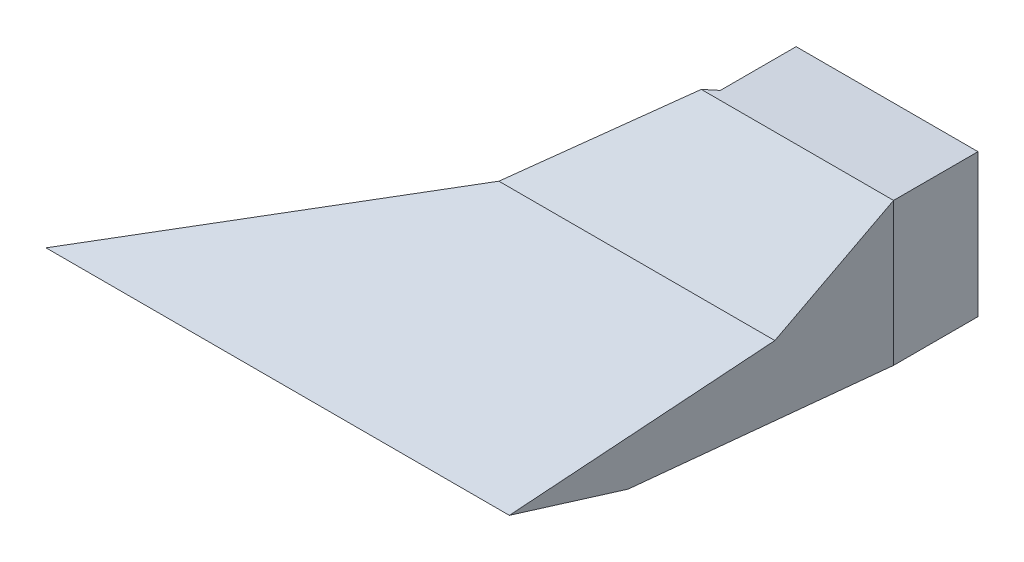
SolidWorks part; units mm, degrees
ref_plane "Front"
ref_plane "Top" through (0, 0, 0) normal (0, 1, 0) x (1, 0, 0)
ref_plane "Right" through (0, 0, 0) normal (1, 0, 0) x (0, 0, -1)
sketch "Side base sketch" plane through (0, 0, 0) normal (-1, 0, 0) x (0, 0, 1)
  line L0 (0, 13.2) -> (8.4913, 5)
  line L1 (0, 0) -> (6, -1)
  line L2 (6, -1) -> (19, -3.1667)
  line L3 (8.4913, 5) -> (19.4913, 0.803)
  line L4 (19.4913, 0.803) -> (27.4913, -2.2493)
  line L5 (27.4913, -2.2493) -> (19, -3.1667)
  line L6 (0, 13.2) -> (0, 0)
  dimension "D1" = 6
  dimension "D2" = 6
  dimension "D3" = 1
  dimension "D4" = 46
  dimension "D5" = 13
  dimension "D6" = 11
  dimension "D7" = 4
  dimension "D8" = 8
  dimension "D9" = 13.2
extrude "Side base" add sketch "Side base sketch" against normal blind 0.8
pattern_linear "Side base 2" count 2 spacing 50 along (1, 0, 0) of bodies 108
sketch "Wall base sketch" plane through (0.8, 0, 0) normal (1, 0, 0) x (0, 0, -1)
  line L0 (0, 12.0879) -> (-8.0533, 4.3109)
  line L1 (-8.0533, 4.3109) -> (-25.7424, -2.4382)
  line L3 (-19, -3.4019) -> (-19, 4.6777) construction
  line L4 (0, 13.2) -> (0, 0) construction
  line L5 (0, 0) -> (-19, -3.1667) construction
  line L8 (-8.4913, 5) -> (0, 13.2) construction
  line L9 (0, 0.811) -> (-19, -2.3556)
  line L11 (-19, -2.3556) -> (-19, -3.1667)
  line L12 (-19, -3.1667) -> (0, 0)
  line L13 (0, 0) -> (0, 0.811)
  line L14 (-25.7424, -2.4382) -> (-27.4913, -2.2493)
  line L15 (-27.4913, -2.2493) -> (-8.4913, 5)
  line L16 (-8.4913, 5) -> (0, 13.2)
  line L17 (0, 13.2) -> (0, 12.0879)
  line L18 (-19, -3.1667) -> (-27.4913, -2.2493) construction
  dimension "D1" = 0.8
  dimension "D2" = 0.8
  dimension "D3" = 0.8
extrude "Front back walls" add sketch "Wall base sketch" along normal up to next (50 mm away)
sketch "Base sketch" plane through (0, 0, 0) normal (0, 0, -1) x (-1, 0, 0)
  line L0 (-50, 12.0879) -> (-0.8, 12.0879) construction
  line L1 (0, 13.2) -> (-50.8, 13.2)
  line L2 (0, 13.2) -> (0, 0)
  line L3 (0, 0) -> (-50.8, 0)
  line L4 (-50.8, 13.2) -> (-50.8, 0)
  line L5 (-50, 0.811) -> (-34.8, 0.811)
  line L6 (-50, 0.811) -> (-50, 12.0879)
  line L7 (-50, 12.0879) -> (-34.8, 12.0879)
  line L8 (-34.8, 0.811) -> (-34.8, 12.0879)
  dimension "D1" = 15.2
extrude "Base" add sketch "Base sketch" along normal blind 0.8
sketch "Attachment base sketch" plane through (0, 0, -0.8) normal (0, 0, -1) x (-1, 0, 0)
  line L0 (-50.8, 0) -> (0, 0) construction
  line L1 (-50.8, 13.2) -> (-34, 13.2)
  line L2 (-50.8, 13.2) -> (-50.8, 0)
  line L3 (-50.8, 0) -> (-34, 0)
  line L4 (-34, 13.2) -> (-34, 0)
  line L5 (-34.8, 0.811) -> (-34.8, 12.0879) construction
  line L7 (-34.8, 12.0879) -> (-50, 12.0879)
  line L8 (-34.8, 12.0879) -> (-34.8, 0.811)
  line L9 (-34.8, 0.811) -> (-50, 0.811)
  line L10 (-50, 12.0879) -> (-50, 0.811)
  dimension "D1" = 0.8
extrude "Attachment base" add sketch "Attachment base sketch" along normal blind 7
sketch "Sketch4" plane through (0.8, 0, 0) normal (1, 0, 0) x (0, 0, -1)
  line L0 (-25.7424, -2.4382) -> (-19, -3.1667)
  line L1 (-19, -3.1667) -> (-19, -2.3556)
  line L2 (-19, -2.3556) -> (0, 0.811)
  line L3 (0, 0.811) -> (0, 12.0879)
  line L4 (-8.0533, 4.3109) -> (0, 12.0879) construction
  line L5 (0, 12.0879) -> (0, 0.811) construction
  line L6 (0, 12.0879) -> (-8.0533, 4.3109)
  line L7 (-8.0533, 4.3109) -> (-25.7424, -2.4382)
extrude "Left right wall removal" cut sketch "Sketch4" against normal through all both and the other way through all
ref_point "Cutaway left intersection point" parameters "D1"=8
ref_plane "Cutaway left plane" through (46.834, 0, 13.6287) normal (0.9602, 0, 0.2794) x (0.2794, 0, -0.9602)
sketch "Sketch6" plane through (46.834, 0, 13.6287) normal (0.9602, 0, 0.2794) x (0.2794, 0, -0.9602)
  line L1 (-14.4376, -3.1667) -> (14.1941, -3.1667)
  line L2 (-14.4376, -3.1667) -> (-14.4376, 13.2)
  line L3 (-14.4376, 13.2) -> (14.1941, 13.2)
  line L4 (14.1941, -3.1667) -> (14.1941, 13.2)
  point P4 (-14.4376, -2.2493)
  point P6 (-5.5941, -3.1667)
extrude "Cutaway left" cut sketch "Sketch6" along normal through all
sketch "Sketch7" plane through (46.834, 0, 13.6287) normal (0.9602, 0, 0.2794) x (0.2794, 0, -0.9602)
  line L0 (-5.5941, -2.3556) -> (-5.5941, -3.1667)
  line L1 (-5.5941, -3.1667) -> (-12.6161, -2.4382)
  line L2 (-12.6161, -2.4382) -> (5.8067, 4.3109)
  line L3 (5.8067, 4.3109) -> (14.1941, 12.0879)
  line L4 (14.1941, 12.0879) -> (14.1941, 0.811)
  line L5 (14.1941, 0.811) -> (-5.5941, -2.3556)
extrude "Left wall" add sketch "Sketch7" along direction (-1, 0, 0) on the side against the normal blind 0.8332
ref_point "Cutaway right intersection point 1" parameters "D1"=4
ref_point "Cutaway right intersection point 2" parameters "D1"=4
ref_plane "Cutaway right plane" through (13.5167, 0, 16.2441) normal (0.6396, 0, 0.7687) x (0.7687, 0, -0.6396)
sketch "Sketch9" plane through (13.5167, 0, 16.2441) normal (0.6396, 0, 0.7687) x (0.7687, 0, -0.6396)
  line L1 (26.6471, 13.2) -> (-17.5841, 13.2)
  line L2 (26.6471, 13.2) -> (26.6471, -3.1667)
  line L3 (26.6471, -3.1667) -> (-17.5841, -3.1667)
  line L4 (-17.5841, 13.2) -> (-17.5841, -3.1667)
extrude "Cutaway right" cut sketch "Sketch9" against normal through all
sketch "Sketch10" plane through (13.5167, 0, 16.2441) normal (-0.6396, 0, -0.7687) x (-0.7687, 0, 0.6396)
  line L0 (-25.3964, 12.0879) -> (-25.3964, 0.811)
  line L1 (-25.3964, 0.811) -> (4.3086, -2.3556)
  line L2 (4.3086, -2.3556) -> (4.3086, -3.1667)
  line L3 (4.3086, -3.1667) -> (14.8498, -2.4382)
  line L4 (14.8498, -2.4382) -> (-12.8057, 4.3109)
  line L5 (-12.8057, 4.3109) -> (-25.3964, 12.0879)
extrude "Right wall" add sketch "Sketch10" along direction (-1, 0, 0) on the side against the normal blind 1.2507
sketch "Sketch11" plane through (0, 0, -7.8) normal (0, 0, -1) x (-1, 0, 0)
  line L0 (-34, 13.2) -> (-50.8, 13.2) construction
  line L1 (-50, 12.0879) -> (-34.8, 12.0879)
  line L2 (-50, 12.0879) -> (-50, 12.4)
  line L3 (-50, 12.4) -> (-34.8, 12.4)
  line L4 (-34.8, 12.0879) -> (-34.8, 12.4)
  dimension "D1" = 0.8
extrude "Pipe top extra cutaway" cut sketch "Sketch11" against normal up to surface (7.8 mm away)
ref_plane "Air flow cut plane" through (0, 0, 27.4913) normal (0, 0, 1) x (1, 0, 0)
sketch "Sketch1" plane through (0, 0, -7.8) normal (0, 0, -1) x (-1, 0, 0)
  line L0 (-50, 12.4) -> (-50, 0.811) construction
  line L1 (-50, 12.4) -> (-34.8, 12.4)
  line L2 (-50, 12.4) -> (-50, 0.811)
  line L3 (-50, 0.811) -> (-34.8, 0.811)
  line L4 (-34.8, 12.4) -> (-34.8, 0.811)
extrude "Fan base" add sketch "Sketch1" along normal blind 0.1 separate body
equation "\"wall_thicknes\"= 0.8"
equation "\"D1@Base\" = \"wall_thicknes\""
equation "\"D1@Wall base sketch\"=\"wall_thicknes\""
equation "\"D1@Side base\"=\"wall_thicknes\""
equation "\"D2@Wall base sketch\"=\"wall_thicknes\""
equation "\"D3@Wall base sketch\"=\"wall_thicknes\""
equation "\"D1@Base sketch\"=\"wall_thicknes\"*-2+16.8"
equation "\"D1@Attachment base sketch\"=\"wall_thicknes\""
equation "\"D1@Left wall\"=\"left_wall_thickness\""
equation "\"D1@Sketch11\"=\"wall_thicknes\""
equation "\"left_wall_thickness\"= 0.83318430202930948562"
equation "\"right_wall_thickness\"= 1.25073472653581935106"
equation "\"D1@Right wall\"=\"right_wall_thickness\""
